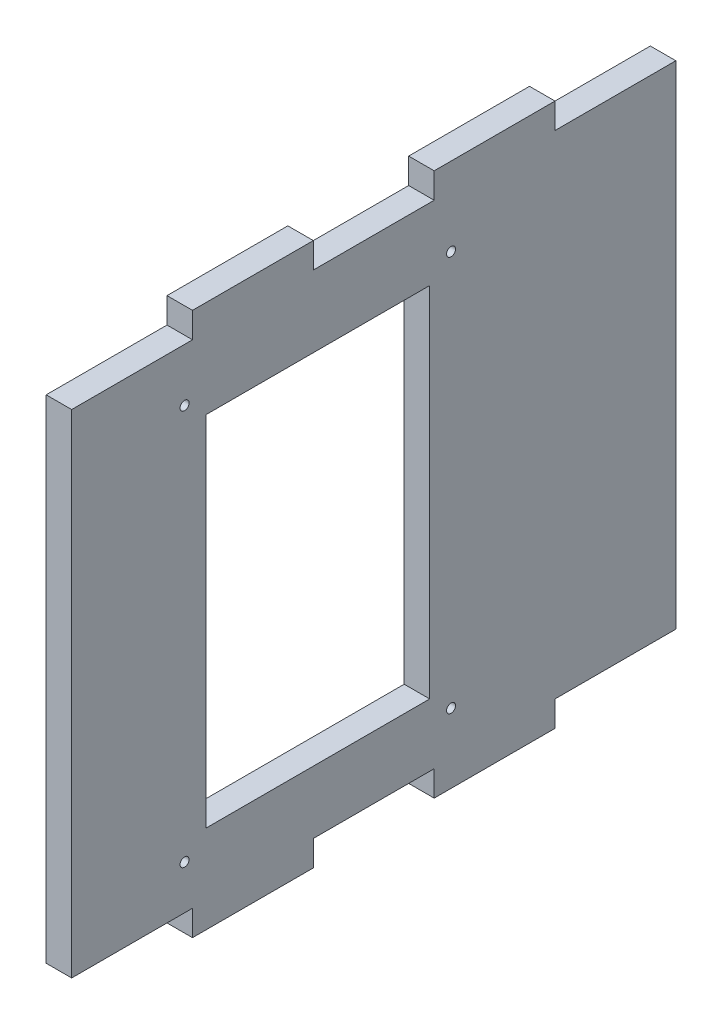
SolidWorks part; units mm, degrees
ref_plane "Front Plane" through (0, 0, 0) normal (0, 0, 1) x (1, 0, 0)
ref_plane "Top Plane" through (0, 0, 0) normal (0, 1, 0) x (1, 0, 0)
ref_plane "Right Plane" through (0, 0, 0) normal (1, 0, 0) x (0, 0, -1)
sketch "Sketch1" plane through (0, 0, 0) normal (1, 0, 0) x (0, 0, -1)
  line L1 (0, 0) -> (135, 0)
  line L2 (0, 0) -> (0, 122)
  line L3 (0, 122) -> (135, 122)
  line L4 (135, 0) -> (135, 122)
sketch "Sketch2" plane through (0, 0, 0) normal (1, 0, 0) x (0, 0, -1)
  line L0 (0, 116) -> (27, 116)
  line L1 (0, 0) -> (0, 122) construction
  line L2 (27, 116) -> (27, 121.7)
  line L4 (27, 121.7) -> (54, 121.7)
  line L5 (54, 121.7) -> (54, 116)
  line L6 (54, 116) -> (81, 116)
  line L7 (81, 116) -> (81, 121.7)
  line L8 (81, 121.7) -> (108, 121.7)
  line L9 (108, 121.7) -> (108, 116)
  line L10 (108, 116) -> (135, 116)
  line L11 (135, 0) -> (135, 122) construction
  line L12 (135, 116) -> (135, 130)
  line L13 (135, 130) -> (0, 130)
  line L14 (0, 130) -> (0, 116)
  line L16 (0, -8) -> (0, 6)
  line L17 (135, -8) -> (0, -8)
  line L18 (135, 6) -> (135, -8)
  line L19 (108, 6) -> (135, 6)
  line L20 (108, 0.3) -> (108, 6)
  line L21 (81, 0.3) -> (108, 0.3)
  line L22 (81, 6) -> (81, 0.3)
  line L23 (54, 6) -> (81, 6)
  line L24 (54, 0.3) -> (54, 6)
  line L25 (27, 0.3) -> (54, 0.3)
  line L26 (27, 6) -> (27, 0.3)
  line L27 (0, 6) -> (27, 6)
extrude "Boss-Extrude1" add sketch "Sketch1" along normal blind 5.7
extrude "Cut-Extrude1" cut sketch "Sketch2" along normal blind 6
sketch "Hole" plane through (0, 0, 0) normal (1, 0, 0) x (0, 0, -1)
  line L0 (80, 100) -> (30, 20) construction
  line L1 (30, 100) -> (80, 100)
  line L2 (30, 100) -> (30, 20)
  line L3 (30, 20) -> (80, 20)
  line L4 (80, 100) -> (80, 20)
  line L5 (30, 100) -> (80, 20) construction
sketch "Screw Locations" plane through (0, 0, 0) normal (1, 0, 0) x (0, 0, -1)
  line L7 (25.23, 15.83) -> (84.77, 15.83) construction
  line L8 (25.23, 15.83) -> (25.23, 104.17) construction
  line L9 (25.23, 104.17) -> (84.77, 104.17) construction
  line L10 (84.77, 15.83) -> (84.77, 104.17) construction
  line L11 (25.23, 15.83) -> (84.77, 104.17) construction
  line L12 (25.23, 104.17) -> (84.77, 15.83) construction
  circle A0 centre (25.23, 104.17) radius 1
  circle A1 centre (84.77, 104.17) radius 1
  circle A2 centre (25.23, 15.83) radius 1
  circle A3 centre (84.77, 15.83) radius 1
  point P4 (55, 60)
sketch "Plate Area" plane through (0, 0, 0) normal (1, 0, 0) x (0, 0, -1)
  line L7 (21.41, 107.94) -> (88.59, 107.94)
  line L8 (21.41, 107.94) -> (21.41, 12.06)
  line L9 (21.41, 12.06) -> (88.59, 12.06)
  line L10 (88.59, 107.94) -> (88.59, 12.06)
  line L11 (21.41, 107.94) -> (88.59, 12.06) construction
  line L12 (21.41, 12.06) -> (88.59, 107.94) construction
  point P5 (55, 60)
extrude "Cut-Extrude2" cut sketch "Hole" along normal blind 70
extrude "Cut-Extrude3" cut sketch "Screw Locations" along normal blind 52
